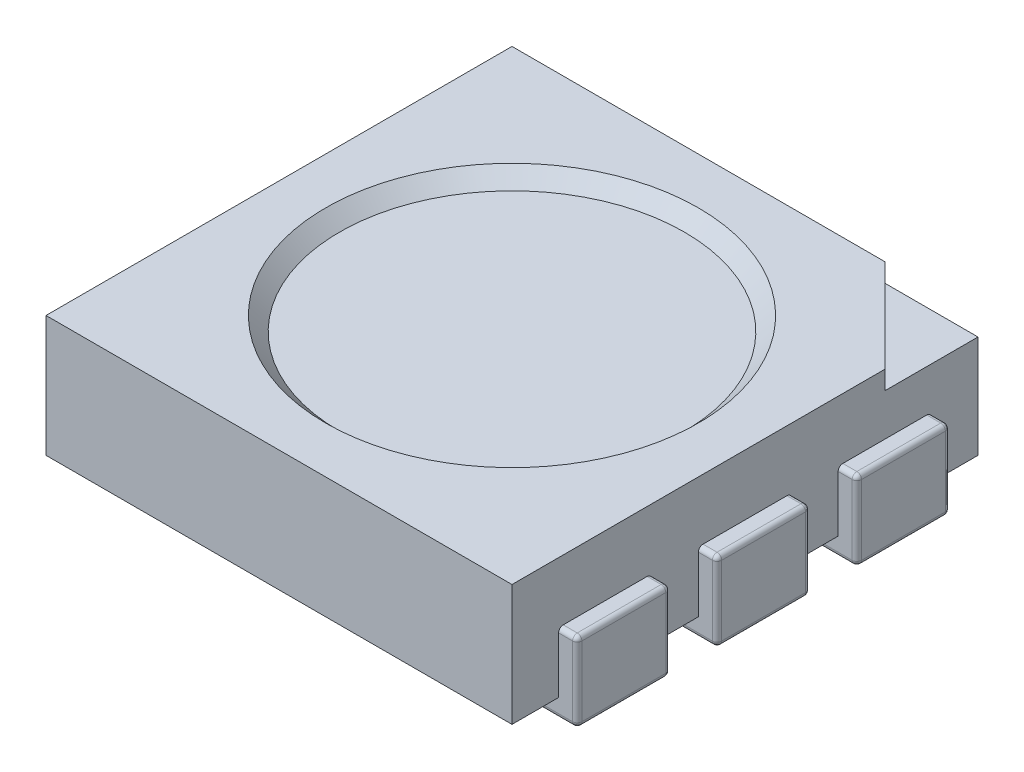
SolidWorks part; units mm, degrees
ref_plane "Front Plane" through (0, 0, 0) normal (0, 0, 1) x (1, 0, 0)
ref_plane "Top Plane" through (0, 0, 0) normal (0, 1, 0) x (1, 0, 0)
ref_plane "Right Plane" through (0, 0, 0) normal (1, 0, 0) x (0, 0, -1)
sketch "Sketch1" plane through (0, 0, 0) normal (0, 1, 0) x (1, 0, 0)
  line L1 (0, 0) -> (5, 0)
  line L2 (0, 0) -> (0, 5)
  line L3 (0, 5) -> (5, 5)
  line L4 (5, 0) -> (5, 5)
  dimension "D1" = 5
  dimension "D2" = 5
extrude "Boss-Extrude1" add sketch "Sketch1" along normal blind 1.3
sketch "Sketch2" plane through (0, 1.3, 0) normal (0, 1, 0) x (1, 0, 0)
  line L0 (5, 5) -> (4, 5)
  line L1 (5, 5) -> (0, 5) construction
  line L2 (4, 5) -> (5, 4)
  line L3 (5, 0) -> (5, 5) construction
  line L4 (5, 4) -> (5, 5)
  dimension "D1" = 1
  dimension "D2" = 1
extrude "Cut-Extrude1" cut sketch "Sketch2" against normal blind 0.2
sketch "Sketch3" plane through (0, 1.3, 0) normal (0, 1, 0) x (1, 0, 0)
  line L0 (0, 5) -> (5, 0) construction
  circle A0 centre (2.5, 2.5) radius 2
  dimension "D1" = 4
extrude "Cut-Extrude2" cut sketch "Sketch3" against normal blind 0.65 draft 45
sketch "Sketch4" plane through (0, 0, 0) normal (0, -1, 0) x (1, 0, 0)
  line L0 (-0.2, -2) -> (1.2, -2)
  line L1 (-0.2, -0.5) -> (1.2, -0.5)
  line L2 (-0.2, -0.5) -> (-0.2, -1.5)
  line L3 (-0.2, -1.5) -> (1.2, -1.5)
  line L4 (1.2, -0.5) -> (1.2, -1.5)
  line L5 (-0.2, -2) -> (-0.2, -3)
  line L6 (-0.2, -3) -> (1.2, -3)
  line L7 (1.2, -2) -> (1.2, -3)
  line L8 (-0.2, -3.5) -> (1.2, -3.5)
  line L9 (-0.2, -3.5) -> (-0.2, -4.5)
  line L10 (-0.2, -4.5) -> (1.2, -4.5)
  line L11 (1.2, -3.5) -> (1.2, -4.5)
  line L12 (0, 0) -> (5, 0) construction
  line L13 (0, -5) -> (0, 0) construction
  line L14 (2.5, 0) -> (2.5, -5) construction
  line L15 (5, -5) -> (0, -5) construction
  line L16 (3.8, -3.5) -> (3.8, -4.5)
  line L17 (5.2, -4.5) -> (3.8, -4.5)
  line L18 (5.2, -3.5) -> (5.2, -4.5)
  line L19 (5.2, -3.5) -> (3.8, -3.5)
  line L20 (3.8, -2) -> (3.8, -3)
  line L21 (5.2, -3) -> (3.8, -3)
  line L22 (5.2, -2) -> (5.2, -3)
  line L23 (3.8, -0.5) -> (3.8, -1.5)
  line L24 (5.2, -1.5) -> (3.8, -1.5)
  line L25 (5.2, -0.5) -> (5.2, -1.5)
  line L26 (5.2, -0.5) -> (3.8, -0.5)
  line L27 (5.2, -2) -> (3.8, -2)
  dimension "D1" = 1
  dimension "D2" = 1.4
  dimension "D4" = 0.5
  dimension "D5" = 0.2
  dimension "D3" = 3
extrude "Boss-Extrude2" add sketch "Sketch4" against normal blind 0.65 and the other way blind 0.2
sketch "Sketch5" plane through (0, 0, 0) normal (0, -1, 0) x (1, 0, 0)
  line L0 (5, 0) -> (0, -5) construction
  line L1 (2.5, 0) -> (2.5, -5) construction
  line L2 (0, 0) -> (5, 0) construction
  line L3 (5, -5) -> (0, -5) construction
  line L4 (-0.2, -2.5) -> (5.2, -2.5) construction
  line L5 (-0.2, -2) -> (-0.2, -3) construction
  line L6 (5.2, -3) -> (5.2, -2) construction
  line L7 (3, -4.6) -> (3, -3.1)
  line L8 (2, -0.4) -> (3, -0.4)
  line L9 (2, -0.4) -> (2, -1.9)
  line L10 (2, -1.9) -> (3, -1.9)
  line L11 (3, -0.4) -> (3, -1.9)
  line L12 (2, -3.1) -> (3, -3.1)
  line L13 (2, -4.6) -> (2, -3.1)
  line L14 (2, -4.6) -> (3, -4.6)
  circle A1 centre (2.5, -2.5) radius 0.5
  dimension "D1" = 1
  dimension "D2" = 1
  dimension "D3" = 0.5
  dimension "D4" = 1.5
  dimension "D5" = 0.6
extrude "Cut-Extrude3" cut sketch "Sketch5" against normal blind 0.1
sketch "Sketch6" plane through (0, 0.1, 0) normal (0, -1, 0) x (1, 0, 0)
  circle A0 centre (2.5, -2.5) radius 0.25
  dimension "D1" = 0.5
extrude "Cut-Extrude4" cut sketch "Sketch6" against normal blind 0.1
sketch "Sketch7" plane through (0, 0.65, 0) normal (0, 1, 0) x (1, 0, 0)
  circle A0 centre (2.5, 2.5) radius 1.35
extrude "Boss-Extrude3" add sketch "Sketch7" along normal blind 0.5 draft 45 draft outward yes
fillet "Fillet2" radius 0.05 66 edges at (4.5, -0.2, -1.5) (3.8, -0.2, -1) (4.5, -0.2, -0.5) (5.2, -0.2, -1) (5.2, 0.225, -0.5) (5.2, 0.65, -1) (5.2, 0.225, -1.5) (3.8, -0.1, -0.5) (3.8, -0.1, -1.5) (5.1, 0.65, -1.5) (5.1, 0.65, -0.5) (4.5, -0.2, -3) (3.8, -0.2, -2.5) (4.5, -0.2, -2) (5.2, 0.225, -3.5) (5.2, 0.65, -4) (5.2, 0.225, -4.5) (5.2, -0.2, -4) (4.5, -0.2, -4.5) (3.8, -0.2, -4) (4.5, -0.2, -3.5) (5.2, -0.2, -2.5) (5.2, 0.225, -2) (5.2, 0.65, -2.5) (5.2, 0.225, -3) (5.1, 0.65, -3.5) (5.1, 0.65, -4.5) (3.8, -0.1, -4.5) (3.8, -0.1, -3.5) (3.8, -0.1, -2) (3.8, -0.1, -3) (5.1, 0.65, -3) (5.1, 0.65, -2) (-0.2, 0.225, -1.5) (-0.2, 0.65, -1) (-0.2, 0.225, -0.5) (0.5, -0.2, -0.5) (1.2, -0.2, -1) (0.5, -0.2, -1.5) (-0.2, -0.2, -1) (-0.2, 0.225, -3) (-0.2, 0.65, -2.5) (-0.2, 0.225, -2) (0.5, -0.2, -2) (1.2, -0.2, -2.5) (0.5, -0.2, -3) (-0.2, -0.2, -2.5) (0.5, -0.2, -3.5) (1.2, -0.2, -4) (0.5, -0.2, -4.5) (-0.2, -0.2, -4) (-0.2, 0.225, -4.5) (-0.2, 0.65, -4) (-0.2, 0.225, -3.5) (1.2, -0.1, -4.5) (1.2, -0.1, -3.5) (1.2, -0.1, -2) (1.2, -0.1, -3) (1.2, -0.1, -1.5) (1.2, -0.1, -0.5) (-0.1, 0.65, -0.5) (-0.1, 0.65, -1.5) (-0.1, 0.65, -2) (-0.1, 0.65, -4.5) (-0.1, 0.65, -3.5) (-0.1, 0.65, -3)
